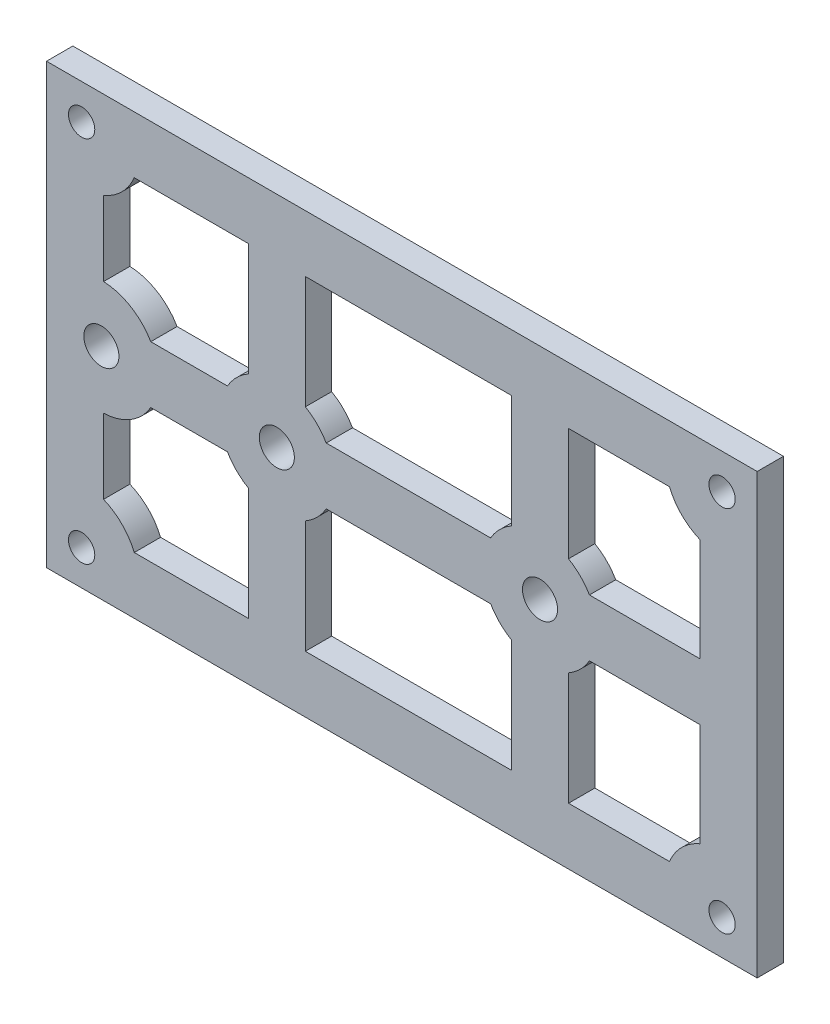
SolidWorks part; units mm, degrees
ref_plane "Front Plane" through (0, 0, 0) normal (0, 0, 1) x (1, 0, 0)
ref_plane "Top Plane" through (0, 0, 0) normal (0, 1, 0) x (1, 0, 0)
ref_plane "Right Plane" through (0, 0, 0) normal (1, 0, 0) x (0, 0, -1)
sketch "Sketch1" plane through (0, 0, 0) normal (0, 0, 1) x (1, 0, 0)
  line L0 (-40.5, 0) -> (40.5, 0) construction
  line L1 (40.5, -25) -> (-40.5, -25)
  line L2 (40.5, -25) -> (40.5, 25)
  line L3 (40.5, 25) -> (-40.5, 25)
  line L4 (-40.5, -25) -> (-40.5, 25)
  line L5 (40.5, -25) -> (-40.5, 25) construction
  line L6 (40.5, 25) -> (-40.5, -25) construction
  circle A0 centre (-34.25, 0) radius 2
  circle A1 centre (-14.25, 0) radius 2
  circle A2 centre (15.75, 0) radius 2
  circle A3 centre (-36.5, 21) radius 1.5
  circle A4 centre (36.5, 21) radius 1.5
  circle A5 centre (36.5, -21) radius 1.5
  circle A6 centre (-36.5, -21) radius 1.5
  point P0 (0, 0)
  dimension "D3" = 4
  dimension "D4" = 6.25
  dimension "D5" = 3
  dimension "D8" = 4
  dimension "D13" = 4
  dimension "D1" = 81
  dimension "D2" = 50
  dimension "D6" = 20
  dimension "D7" = 30
  dimension "D9" = 4
  dimension "D10" = 4
  dimension "D11" = 4
extrude "Boss-Extrude1" add sketch "Sketch1" along normal blind 3
sketch "Sketch3" plane through (0, 0, 3) normal (0, 0, 1) x (1, 0, 0)
  line L0 (30.5, 18.5) -> (19, 18.5)
  line L1 (40.5, 25) -> (-40.5, 25) construction
  line L2 (34, 15) -> (34, 3.25)
  line L3 (40.5, -25) -> (40.5, 25) construction
  line L4 (12.5, 5.6292) -> (12.5, 18.5)
  line L5 (19, 5.6292) -> (19, 18.5)
  line L6 (21.3792, 3.25) -> (34, 3.25)
  line L7 (-40.5, 0) -> (40.5, 0) construction
  line L8 (-40.5, 25) -> (-40.5, -25) construction
  line L9 (12.5, 18.5) -> (-11, 18.5)
  line L11 (-8.6208, 3.25) -> (10.1208, 3.25)
  line L12 (-28.6208, 3.25) -> (-19.8792, 3.25)
  line L13 (-17.5, 5.6292) -> (-17.5, 18.5)
  line L14 (-17.5, 18.5) -> (-30.5, 18.5)
  line L15 (-34, 15) -> (-34, 6.4952)
  line L16 (-11, 18.5) -> (-11, 5.6292)
  line L17 (-14.25, 0) -> (-14.25, 15) construction
  line L18 (15.75, 0) -> (15.75, 21) construction
  circle A0 centre (36.5, 21) radius 6.5 construction
  arc A1 (30.5, 18.5) -> (34, 15) centre (36.5, 21) ccw
  circle A2 centre (15.75, 0) radius 6.5 construction
  arc A3 (19, 5.6292) -> (21.3792, 3.25) centre (15.75, 0) cw
  arc A4 (12.5, 5.6292) -> (10.1208, 3.25) centre (15.75, 0) ccw
  circle A5 centre (-14.25, 0) radius 6.5 construction
  circle A7 centre (-34.25, 0) radius 6.5 construction
  arc A9 (-28.6208, 3.25) -> (-34, 6.4952) centre (-34.25, 0) ccw
  arc A10 (-19.8792, 3.25) -> (-17.5, 5.6292) centre (-14.25, 0) cw
  arc A11 (-11, 5.6292) -> (-8.6208, 3.25) centre (-14.25, 0) cw
  circle A12 centre (-36.5, 21) radius 6.5 construction
  arc A13 (-34, 15) -> (-30.5, 18.5) centre (-36.5, 21) ccw
  dimension "D1" = 13
  dimension "D4" = 6.5
  dimension "D7" = 6.5
  dimension "D2" = 6.5
  dimension "D3" = 6.5
  dimension "D5" = 3.25
  dimension "D6" = 6.5
extrude "Cut-Extrude1" cut sketch "Sketch3" against normal through all
mirror "Mirror2" about plane through (0, 0, 0) normal (0, 1, 0) of "Cut-Extrude1"
